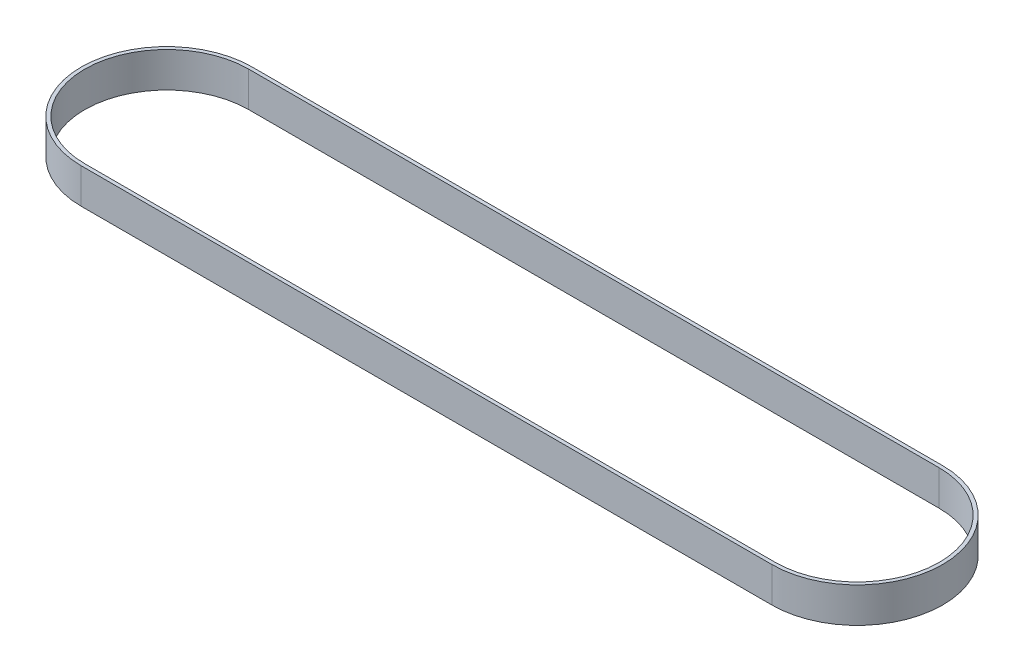
SolidWorks part; units mm, degrees
ref_plane "Front Plane" through (0, 0, 0) normal (0, 0, 1) x (1, 0, 0)
ref_plane "Top Plane" through (0, 0, 0) normal (0, 1, 0) x (1, 0, 0)
ref_plane "Right Plane" through (0, 0, 0) normal (1, 0, 0) x (0, 0, -1)
sketch "Sketch1" plane through (0, 0, 0) normal (0, 1, 0) x (1, 0, 0)
  line L0 (0, 0) -> (295.0718, 0) construction
  line L1 (0, 35.0139) -> (295.0718, 35.0139)
  line L2 (0, -35.0139) -> (295.0718, -35.0139)
  line L3 (0, -36.5379) -> (295.0718, -36.5379)
  line L4 (0, 36.5379) -> (295.0718, 36.5379)
  arc A0 (0, 35.0139) -> (0, -35.0139) centre (0, 0) ccw
  arc A1 (295.0718, -35.0139) -> (295.0718, 35.0139) centre (295.0718, 0) ccw
  arc A2 (0, 36.5379) -> (0, -36.5379) centre (0, 0) ccw
  arc A3 (295.0718, -36.5379) -> (295.0718, 36.5379) centre (295.0718, 0) ccw
  dimension "D2" = 70.0278
  dimension "D3" = 295.0718
  dimension "D4" = 1.524
extrude "Boss-Extrude1" add sketch "Sketch1" along normal blind 15
